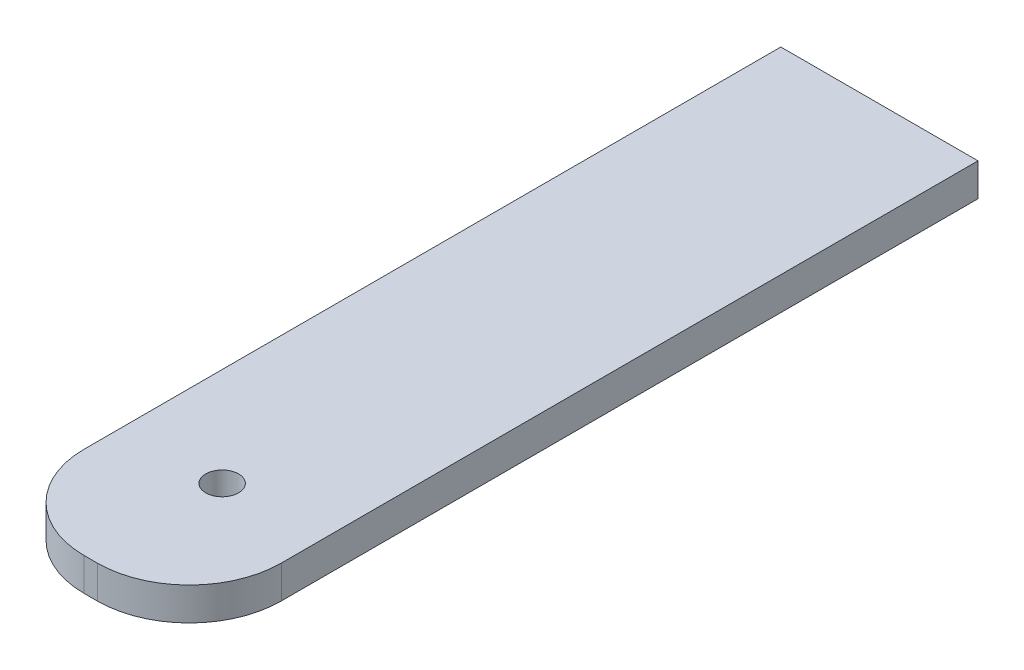
SolidWorks part; units mm, degrees
ref_plane "Front Plane" through (0, 0, 0) normal (0, 0, 1) x (1, 0, 0)
ref_plane "Top Plane" through (0, 0, 0) normal (0, 1, 0) x (1, 0, 0)
ref_plane "Right Plane" through (0, 0, 0) normal (1, 0, 0) x (0, 0, -1)
sketch "Sketch2" plane through (0, 0, 0) normal (0, 1, 0) x (1, 0, 0)
  line L1 (-9.525, 38.1) -> (9.525, 38.1)
  line L2 (-9.525, 38.1) -> (-9.525, -38.1)
  line L3 (-9.525, -38.1) -> (9.525, -38.1)
  line L4 (9.525, 38.1) -> (9.525, -38.1)
  circle A0 centre (0, -25.4) radius 1.5875
  point P6 (0, -38.1)
  point P7 (9.525, 0)
  point P8 (0, 38.1)
  dimension "D3" = 3.175
  dimension "D1" = 19.05
  dimension "D2" = 76.2
  dimension "D4" = 12.7
extrude "Boss-Extrude1" add sketch "Sketch2" along normal blind 3.175
fillet "Fillet1" radius 8.89 1 edges at (9.525, 1.5875, 38.1)
fillet "Fillet2" radius 8.89 1 edges at (-9.525, 1.5875, 38.1)
